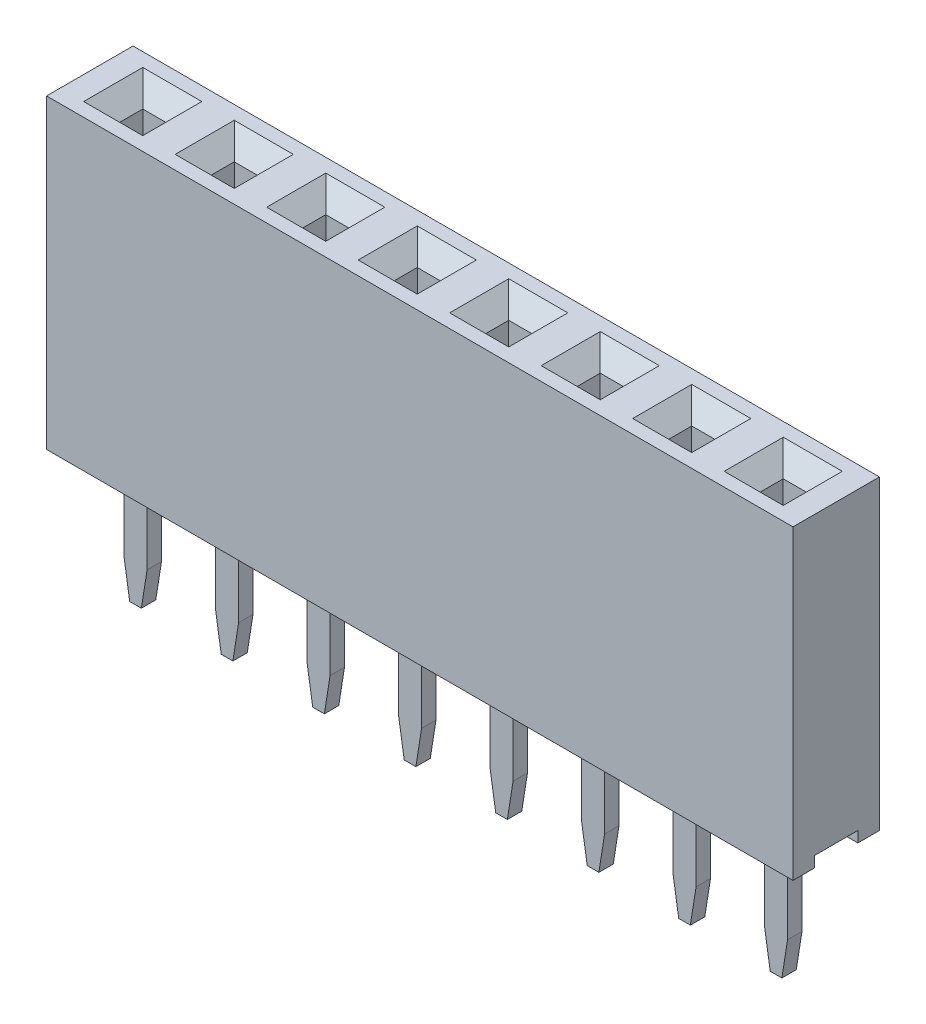
SolidWorks part; units mm, degrees
ref_plane "Front Plane" through (0, 0, 0) normal (0, 0, 1) x (1, 0, 0)
ref_plane "Top Plane" through (0, 0, 0) normal (0, 1, 0) x (1, 0, 0)
ref_plane "Right Plane" through (0, 0, 0) normal (1, 0, 0) x (0, 0, -1)
sketch "Sketch1" plane through (0, 0, 0) normal (0, 1, 0) x (1, 0, 0)
  line L1 (0, 0) -> (20.72, 0)
  line L2 (0, 0) -> (0, 2.4)
  line L3 (0, 2.4) -> (20.72, 2.4)
  line L4 (20.72, 0) -> (20.72, 2.4)
  dimension "D1" = 2.4
  dimension "D2" = 20.72
extrude "Boss-Extrude1" add sketch "Sketch1" along normal blind 8.5
sketch "Sketch3" plane through (0, 0, 0) normal (0, -1, 0) x (1, 0, 0)
  line L0 (0, -1.2) -> (20.72, -1.2) construction
  line L1 (0, -2.4) -> (0, 0) construction
  line L2 (20.72, 0) -> (20.72, -2.4) construction
  line L4 (0, -1.8) -> (20.72, -1.8)
  line L5 (0, -1.8) -> (0, -0.6)
  line L6 (0, -0.6) -> (20.72, -0.6)
  line L7 (20.72, -1.8) -> (20.72, -0.6)
  line L8 (0, -1.8) -> (20.72, -0.6) construction
  line L9 (0, -0.6) -> (20.72, -1.8) construction
  point P6 (10.36, -1.2)
  dimension "D1" = 1.2
extrude "Cut-Extrude1" cut sketch "Sketch3" against normal blind 0.3
sketch "Sketch4" plane through (0, 8.5, 0) normal (0, 1, 0) x (1, 0, 0)
  line L0 (0, 1.2) -> (20.72, 1.2) construction
  line L1 (0, 2.4) -> (0, 0) construction
  line L2 (20.72, 0) -> (20.72, 2.4) construction
  line L3 (3.69, 0.88) -> (3.69, 1.52)
  line L4 (1.15, 0.88) -> (1.79, 0.88)
  line L5 (1.15, 0.88) -> (1.15, 1.52)
  line L6 (1.15, 1.52) -> (1.79, 1.52)
  line L7 (1.79, 0.88) -> (1.79, 1.52)
  line L8 (1.15, 0.88) -> (1.79, 1.52) construction
  line L9 (1.15, 1.52) -> (1.79, 0.88) construction
  line L10 (3.69, 0.88) -> (4.33, 0.88)
  line L11 (4.33, 0.88) -> (4.33, 1.52)
  line L12 (3.69, 1.52) -> (4.33, 1.52)
  line L13 (6.23, 0.88) -> (6.23, 1.52)
  line L14 (6.23, 0.88) -> (6.87, 0.88)
  line L15 (6.87, 0.88) -> (6.87, 1.52)
  line L16 (6.23, 1.52) -> (6.87, 1.52)
  line L17 (8.77, 0.88) -> (8.77, 1.52)
  line L18 (8.77, 0.88) -> (9.41, 0.88)
  line L19 (9.41, 0.88) -> (9.41, 1.52)
  line L20 (8.77, 1.52) -> (9.41, 1.52)
  line L21 (11.31, 0.88) -> (11.31, 1.52)
  line L22 (11.31, 0.88) -> (11.95, 0.88)
  line L23 (11.95, 0.88) -> (11.95, 1.52)
  line L24 (11.31, 1.52) -> (11.95, 1.52)
  line L25 (13.85, 0.88) -> (13.85, 1.52)
  line L26 (13.85, 0.88) -> (14.49, 0.88)
  line L27 (14.49, 0.88) -> (14.49, 1.52)
  line L28 (13.85, 1.52) -> (14.49, 1.52)
  line L29 (16.39, 0.88) -> (16.39, 1.52)
  line L30 (16.39, 0.88) -> (17.03, 0.88)
  line L31 (17.03, 0.88) -> (17.03, 1.52)
  line L32 (16.39, 1.52) -> (17.03, 1.52)
  line L33 (18.93, 0.88) -> (18.93, 1.52)
  line L34 (18.93, 0.88) -> (19.57, 0.88)
  line L35 (19.57, 0.88) -> (19.57, 1.52)
  line L36 (18.93, 1.52) -> (19.57, 1.52)
  line L37 (1.15, 0.88) -> (3.69, 0.88) construction
  point P6 (1.47, 1.2)
  dimension "D1" = 0.64
  dimension "D2" = 0.64
  dimension "D3" = 1.47
  dimension "D5" = 2.54
  dimension "D4" = 8
extrude "Cut-Extrude2" cut sketch "Sketch4" against normal blind 6
chamfer "Chamfer2" distance 0.5 angle 45 32 edges at (1.47, 8.5, -1.52) (1.15, 8.5, -1.2) (1.47, 8.5, -0.88) (1.79, 8.5, -1.2) (4.01, 8.5, -1.52) (3.69, 8.5, -1.2) (4.01, 8.5, -0.88) (4.33, 8.5, -1.2) (6.55, 8.5, -1.52) (6.23, 8.5, -1.2) (6.55, 8.5, -0.88) (6.87, 8.5, -1.2) (8.77, 8.5, -1.2) (9.09, 8.5, -0.88) (9.41, 8.5, -1.2) (9.09, 8.5, -1.52) (11.63, 8.5, -1.52) (11.31, 8.5, -1.2) (11.63, 8.5, -0.88) (11.95, 8.5, -1.2) (14.49, 8.5, -1.2) (14.17, 8.5, -1.52) (13.85, 8.5, -1.2) (14.17, 8.5, -0.88) (16.71, 8.5, -1.52) (16.39, 8.5, -1.2) (16.71, 8.5, -0.88) (17.03, 8.5, -1.2) (19.57, 8.5, -1.2) (19.25, 8.5, -1.52) (18.93, 8.5, -1.2) (19.25, 8.5, -0.88)
sketch "Sketch5" plane through (0, 0.3, 0) normal (0, -1, 0) x (1, 0, 0)
  line L0 (0, -1.2) -> (20.72, -1.2) construction
  line L1 (0, -0.6) -> (0, -1.8) construction
  line L2 (20.72, -1.8) -> (20.72, -0.6) construction
  line L3 (3.69, -1.4) -> (3.69, -1)
  line L4 (1.15, -1.4) -> (1.79, -1.4)
  line L5 (1.15, -1.4) -> (1.15, -1)
  line L6 (1.15, -1) -> (1.79, -1)
  line L7 (1.79, -1.4) -> (1.79, -1)
  line L8 (1.15, -1.4) -> (1.79, -1) construction
  line L9 (1.15, -1) -> (1.79, -1.4) construction
  line L10 (3.69, -1.4) -> (4.33, -1.4)
  line L11 (4.33, -1.4) -> (4.33, -1)
  line L12 (3.69, -1) -> (4.33, -1)
  line L13 (6.23, -1.4) -> (6.23, -1)
  line L14 (6.23, -1.4) -> (6.87, -1.4)
  line L15 (6.87, -1.4) -> (6.87, -1)
  line L16 (6.23, -1) -> (6.87, -1)
  line L17 (8.77, -1.4) -> (8.77, -1)
  line L18 (8.77, -1.4) -> (9.41, -1.4)
  line L19 (9.41, -1.4) -> (9.41, -1)
  line L20 (8.77, -1) -> (9.41, -1)
  line L21 (11.31, -1.4) -> (11.31, -1)
  line L22 (11.31, -1.4) -> (11.95, -1.4)
  line L23 (11.95, -1.4) -> (11.95, -1)
  line L24 (11.31, -1) -> (11.95, -1)
  line L25 (13.85, -1.4) -> (13.85, -1)
  line L26 (13.85, -1.4) -> (14.49, -1.4)
  line L27 (14.49, -1.4) -> (14.49, -1)
  line L28 (13.85, -1) -> (14.49, -1)
  line L29 (16.39, -1.4) -> (16.39, -1)
  line L30 (16.39, -1.4) -> (17.03, -1.4)
  line L31 (17.03, -1.4) -> (17.03, -1)
  line L32 (16.39, -1) -> (17.03, -1)
  line L33 (18.93, -1.4) -> (18.93, -1)
  line L34 (18.93, -1.4) -> (19.57, -1.4)
  line L35 (19.57, -1.4) -> (19.57, -1)
  line L36 (18.93, -1) -> (19.57, -1)
  line L37 (1.15, -1.4) -> (3.69, -1.4) construction
  point P6 (1.47, -1.2)
  dimension "D1" = 0.4
  dimension "D2" = 0.64
  dimension "D3" = 1.47
  dimension "D5" = 2.54
  dimension "D4" = 8
extrude "Boss-Extrude2" add sketch "Sketch5" along normal blind 3.8
chamfer "Chamfer3" distance 1 angle 9 16 edges at (19.57, -3.5, -1.2) (18.93, -3.5, -1.2) (17.03, -3.5, -1.2) (16.39, -3.5, -1.2) (14.49, -3.5, -1.2) (13.85, -3.5, -1.2) (11.95, -3.5, -1.2) (11.31, -3.5, -1.2) (9.41, -3.5, -1.2) (8.77, -3.5, -1.2) (6.87, -3.5, -1.2) (6.23, -3.5, -1.2) (4.33, -3.5, -1.2) (3.69, -3.5, -1.2) (1.79, -3.5, -1.2) (1.15, -3.5, -1.2)
